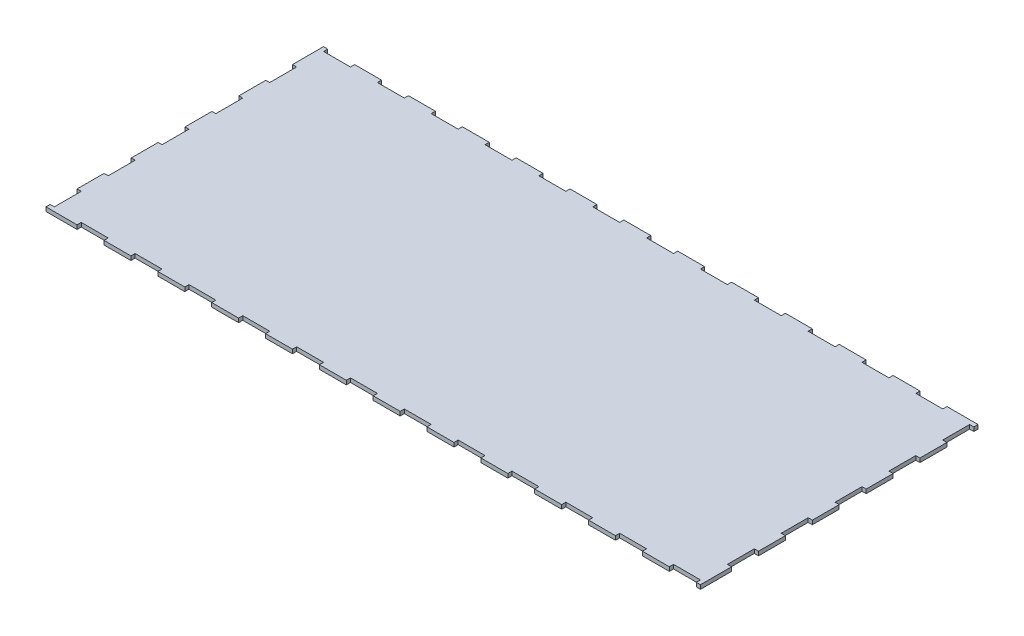
SolidWorks part; units mm, degrees
material "Acrílico (Impacto medio-alto)"
ref_plane "Alzado" through (0, 0, 0) normal (0, 0, 1) x (1, 0, 0)
ref_plane "Planta" through (0, 0, 0) normal (0, 1, 0) x (1, 0, 0)
ref_plane "Vista lateral" through (0, 0, 0) normal (1, 0, 0) x (0, 0, -1)
sketch "Croquis1" plane through (0, 0, 0) normal (0, 1, 0) x (1, 0, 0)
  line L0 (0, 200) -> (-3.1, 200)
  line L3 (0, 200) -> (480, 200)
  line L5 (-3.1, 200) -> (-3.1, 180)
  line L6 (-3.1, 180) -> (0, 180)
  line L7 (0, 119.9963) -> (0, 139.9963)
  line L8 (0, 119.9963) -> (-2.9, 119.9963)
  line L9 (-2.9, 119.9963) -> (-2.9, 99.9963)
  line L10 (-2.9, 99.9963) -> (0, 99.9963) construction
  line L11 (0, 99.9963) -> (0, 80)
  line L12 (0, 80) -> (-2.9, 80)
  line L13 (-2.9, 80) -> (-2.9, 60)
  line L14 (-2.9, 60) -> (0, 60)
  line L15 (0, 60) -> (0, 40)
  line L16 (0, 0) -> (0, 20)
  line L17 (0, 40) -> (-3.1, 40)
  line L18 (-3.1, 40) -> (-3.1, 20)
  line L19 (-3.1, 20) -> (0, 20)
  line L20 (0, 0) -> (0, -3.1)
  line L21 (0, -3.1) -> (20, -3.1)
  line L22 (20, -3.1) -> (20, 0)
  line L23 (20, 0) -> (40, 0)
  line L24 (0, 0) -> (480, 0)
  line L26 (40, 0) -> (40, -3.1)
  line L27 (40, -3.1) -> (60, -3.1)
  line L28 (60, -3.1) -> (60, 0)
  line L29 (60, 0) -> (80, 0)
  line L30 (80, 0) -> (80, -3.1)
  line L31 (80, -3.1) -> (100, -3.1)
  line L32 (100, -3.1) -> (100, 0)
  line L33 (100, 0) -> (120, 0)
  line L34 (120, 0) -> (120, -3.1)
  line L35 (120, -3.1) -> (140, -3.1)
  line L36 (140, -3.1) -> (140, 0)
  line L37 (140, 0) -> (160, 0)
  line L38 (160, 0) -> (160, -3.1)
  line L39 (160, -3.1) -> (180, -3.1)
  line L40 (180, -3.1) -> (180, 0)
  line L41 (180, 0) -> (200, 0)
  line L42 (200, 0) -> (200, -3.1)
  line L43 (200, -3.1) -> (220, -3.1)
  line L44 (220, -3.1) -> (220, 0)
  line L45 (220, 0) -> (240, 0)
  line L46 (240, 0) -> (240, -3.1)
  line L47 (240, -3.1) -> (260, -3.1)
  line L48 (260, -3.1) -> (260, 0)
  line L49 (260, 0) -> (280, 0)
  line L50 (280, 0) -> (280, -3.1)
  line L51 (280, -3.1) -> (300, -3.1)
  line L52 (300, -3.1) -> (300, 0)
  line L53 (300, 0) -> (320, 0)
  line L54 (320, 0) -> (320, -3.1)
  line L55 (320, -3.1) -> (340, -3.1)
  line L56 (340, -3.1) -> (340, 0)
  line L57 (340, 0) -> (360, 0)
  line L58 (360, 0) -> (360, -3.1)
  line L59 (360, -3.1) -> (380, -3.1)
  line L60 (380, -3.1) -> (380, 0)
  line L61 (380, 0) -> (400, 0)
  line L62 (400, 0) -> (400, -3.1)
  line L63 (400, -3.1) -> (420, -3.1)
  line L64 (420, -3.1) -> (420, 0)
  line L65 (420, 0) -> (440, 0)
  line L66 (440, 0) -> (440, -3.1)
  line L67 (440, -3.1) -> (460, -3.1)
  line L68 (460, -3.1) -> (460, 0)
  line L69 (460, 0) -> (480, 0)
  line L70 (480, 0) -> (483.1, 0)
  line L71 (480, 140) -> (480, 160)
  line L72 (483.1, 140) -> (483.1, 119.9963)
  line L73 (483.1, 180) -> (483.1, 159.9963)
  line L74 (483.1, 140) -> (480, 140)
  line L75 (483.1, 119.9963) -> (480, 119.9963)
  line L76 (480, 100) -> (480, 120)
  line L77 (483.1, 159.9963) -> (480, 159.9963)
  line L78 (483.1, 100) -> (483.1, 79.9963)
  line L79 (483.1, 100) -> (480, 100)
  line L80 (483.1, 79.9963) -> (480, 79.9963)
  line L81 (480, 60) -> (480, 80)
  line L82 (483.1, 60) -> (483.1, 39.9963)
  line L83 (483.1, 60) -> (480, 60)
  line L84 (483.1, 180) -> (480, 180)
  line L85 (480, 180) -> (480, 200)
  line L86 (480, 200) -> (480, 203.1)
  line L87 (480, 203.1) -> (460, 203.1)
  line L88 (460, 203.1) -> (460, 200)
  line L89 (460, 200) -> (440, 200)
  line L90 (420, 200) -> (400, 200)
  line L91 (440, 203.1) -> (420, 203.1)
  line L92 (420, 203.1) -> (420, 200)
  line L93 (440, 200) -> (440, 203.1)
  line L94 (380, 200) -> (360, 200)
  line L95 (400, 203.1) -> (380, 203.1)
  line L96 (380, 203.1) -> (380, 200)
  line L97 (400, 200) -> (400, 203.1)
  line L98 (340, 200) -> (320, 200)
  line L99 (360, 203.1) -> (340, 203.1)
  line L100 (340, 203.1) -> (340, 200)
  line L101 (360, 200) -> (360, 203.1)
  line L102 (300, 200) -> (280, 200)
  line L103 (320, 203.1) -> (300, 203.1)
  line L104 (300, 203.1) -> (300, 200)
  line L105 (320, 200) -> (320, 203.1)
  line L106 (260, 200) -> (240, 200)
  line L107 (280, 203.1) -> (260, 203.1)
  line L108 (260, 203.1) -> (260, 200)
  line L109 (280, 200) -> (280, 203.1)
  line L110 (220, 200) -> (200, 200)
  line L111 (240, 203.1) -> (220, 203.1)
  line L112 (220, 203.1) -> (220, 200)
  line L113 (240, 200) -> (240, 203.1)
  line L114 (180, 200) -> (160, 200)
  line L115 (200, 203.1) -> (180, 203.1)
  line L116 (180, 203.1) -> (180, 200)
  line L117 (200, 200) -> (200, 203.1)
  line L118 (140, 200) -> (120, 200)
  line L119 (160, 203.1) -> (140, 203.1)
  line L120 (140, 203.1) -> (140, 200)
  line L121 (160, 200) -> (160, 203.1)
  line L122 (100, 200) -> (80, 200)
  line L123 (120, 203.1) -> (100, 203.1)
  line L124 (100, 203.1) -> (100, 200)
  line L125 (120, 200) -> (120, 203.1)
  line L126 (60, 200) -> (40, 200)
  line L127 (80, 203.1) -> (60, 203.1)
  line L128 (60, 203.1) -> (60, 200)
  line L129 (80, 200) -> (80, 203.1)
  line L130 (20, 200) -> (0, 200)
  line L131 (40, 203.1) -> (20, 203.1)
  line L132 (20, 203.1) -> (20, 200)
  line L133 (40, 200) -> (40, 203.1)
  line L134 (0, 0) -> (-3.1, 0)
  line L135 (-3.1, 0) -> (-3.1, -3.1)
  line L136 (-3.1, -3.1) -> (0, -3.1)
  line L137 (480, 0) -> (480, -3.1)
  line L138 (480, -3.1) -> (483.1, -3.1)
  line L139 (483.1, -3.1) -> (483.1, 0)
  line L140 (480, 203.1) -> (483.1, 203.1)
  line L141 (483.1, 203.1) -> (483.1, 200)
  line L142 (483.1, 200) -> (480, 200)
  line L143 (-3.1, 200) -> (-3.1, 203.1)
  line L144 (-3.1, 203.1) -> (0, 203.1)
  line L145 (0, 203.1) -> (0, 200)
  line L146 (0, 139.9963) -> (-2.9, 139.9963)
  line L147 (-2.9, 139.9963) -> (-2.9, 159.9963)
  line L148 (0, 180) -> (0, 159.9963)
  line L149 (0, 159.9963) -> (-2.9, 159.9963)
  line L150 (483.1, 39.9963) -> (480, 39.9963)
  line L153 (480, 20) -> (480, 40)
  line L156 (483.1, 20) -> (483.1, -0.0037)
  line L158 (483.1, 20) -> (480, 20)
  line L159 (483.1, -0.0037) -> (480, -0.0037)
  dimension "D1" = 12
  dimension "D2" = 5
  dimension "D3" = 12
extrude "Saliente-Extruir1" add sketch "Croquis1" along normal blind 3
